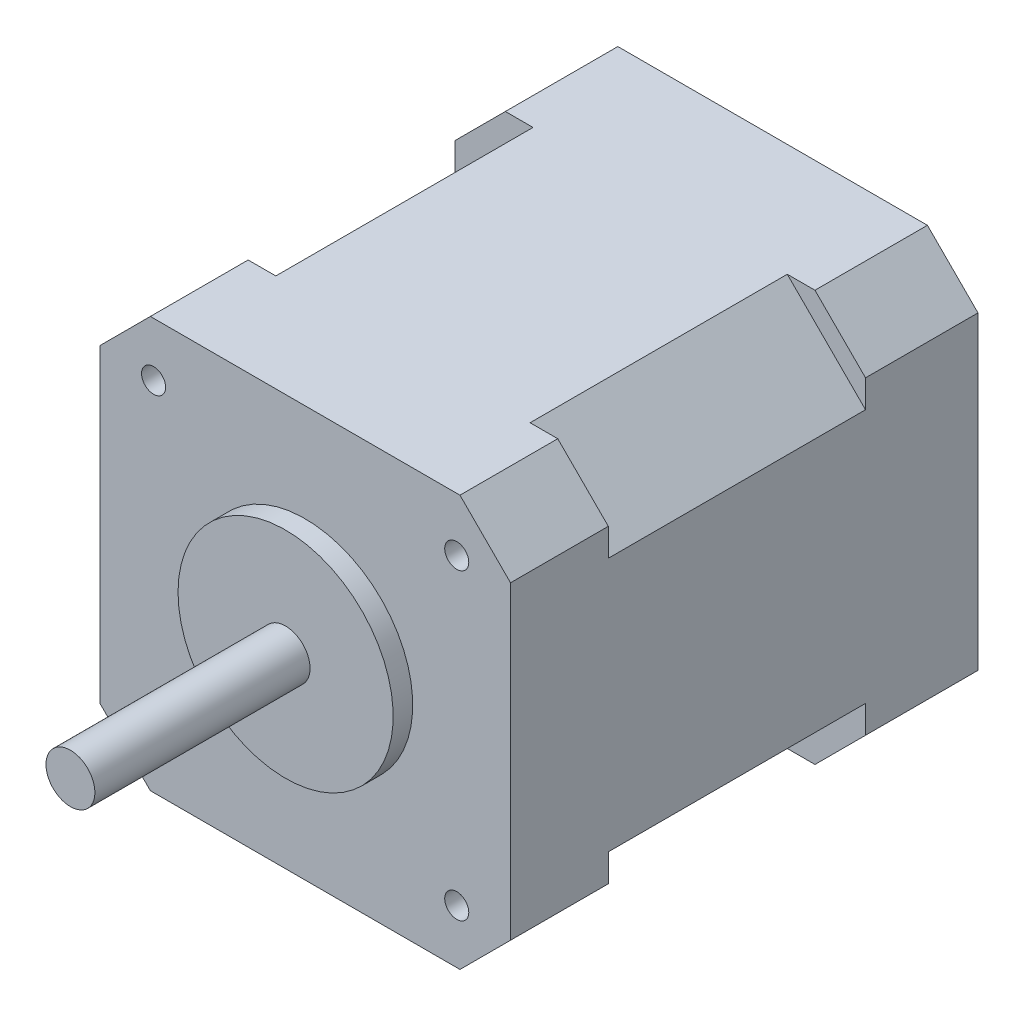
SolidWorks part; units mm, degrees
ref_plane "Front Plane" through (0, 0, 0) normal (0, 0, 1) x (1, 0, 0)
ref_plane "Top Plane" through (0, 0, 0) normal (0, 1, 0) x (1, 0, 0)
ref_plane "Right Plane" through (0, 0, 0) normal (1, 0, 0) x (0, 0, -1)
ref_plane "Plane1" through (0, 0, 0) normal (0, 0, -1) x (-1, 0, 0)
sketch "Sketch1" plane through (0, 0, 0) normal (0, 0, -1) x (-1, 0, 0)
  line L0 (-15.8284, 21) -> (-21, 15.8284)
  line L1 (-21, 15.8284) -> (-21, -15.8284)
  line L2 (-21, -15.8284) -> (-15.8284, -21)
  line L3 (-15.8284, -21) -> (15.8284, -21)
  line L4 (15.8284, -21) -> (21, -15.8284)
  line L5 (21, -15.8284) -> (21, 15.8284)
  line L6 (21, 15.8284) -> (15.8284, 21)
  line L7 (15.8284, 21) -> (-15.8284, 21)
extrude "Boss-Extrude1" add sketch "Sketch1" against normal blind 11.5
sketch "Sketch2" plane through (0, 0, 11.5) normal (0, 0, 1) x (1, 0, 0)
  line L0 (13, -21) -> (-13, -21)
  line L1 (-13, -21) -> (-21, -13)
  line L2 (-21, -13) -> (-21, 13)
  line L3 (-21, 13) -> (-13, 21)
  line L4 (-13, 21) -> (13, 21)
  line L5 (13, 21) -> (21, 13)
  line L6 (21, 13) -> (21, -13)
  line L7 (21, -13) -> (13, -21)
extrude "Boss-Extrude2" add sketch "Sketch2" along normal blind 26.3
sketch "Sketch3" plane through (0, 0, 37.8) normal (0, 0, 1) x (1, 0, 0)
  line L0 (15.8284, 21) -> (21, 15.8284)
  line L1 (21, 15.8284) -> (21, -15.8284)
  line L2 (21, -15.8284) -> (15.8284, -21)
  line L3 (15.8284, -21) -> (-15.8284, -21)
  line L4 (-15.8284, -21) -> (-21, -15.8284)
  line L5 (-21, -15.8284) -> (-21, 15.8284)
  line L6 (-21, 15.8284) -> (-15.8284, 21)
  line L7 (-15.8284, 21) -> (15.8284, 21)
extrude "Boss-Extrude3" add sketch "Sketch3" along normal blind 10
ref_plane "Plane2" through (0, 0, 3.65) normal (0, 0, 1) x (1, 0, 0)
sketch "Sketch4" plane through (0, 0, 3.65) normal (0, 0, 1) x (1, 0, 0)
  line L0 (-31, 1.25) -> (-31, 0.65)
  line L1 (-31, 0.65) -> (-21, 0.65)
  line L2 (-21, 0.65) -> (-21, 1.25)
  line L3 (-21, 1.25) -> (-31, 1.25)
  line L4 (-31, 0.65) -> (-21, 0.65) construction
revolve "Revolve1" add sketch "Sketch4" angle 360 about L4
sketch "Sketch5" plane through (0, 0, 3.65) normal (0, 0, 1) x (1, 0, 0)
  line L0 (-31, -0.05) -> (-31, -0.65)
  line L1 (-31, -0.65) -> (-21, -0.65)
  line L2 (-21, -0.65) -> (-21, -0.05)
  line L3 (-21, -0.05) -> (-31, -0.05)
  line L4 (-31, -0.65) -> (-21, -0.65) construction
revolve "Revolve2" add sketch "Sketch5" angle 360 about L4
ref_plane "Plane3" through (0, 0, 4.95) normal (0, 0, 1) x (1, 0, 0)
sketch "Sketch6" plane through (0, 0, 4.95) normal (0, 0, 1) x (1, 0, 0)
  line L0 (-31, -0.05) -> (-31, -0.65)
  line L1 (-31, -0.65) -> (-21, -0.65)
  line L2 (-21, -0.65) -> (-21, -0.05)
  line L3 (-21, -0.05) -> (-31, -0.05)
  line L4 (-31, -0.65) -> (-21, -0.65) construction
revolve "Revolve3" add sketch "Sketch6" angle 360 about L4
sketch "Sketch7" plane through (0, 0, 4.95) normal (0, 0, 1) x (1, 0, 0)
  line L0 (-31, 1.25) -> (-31, 0.65)
  line L1 (-31, 0.65) -> (-21, 0.65)
  line L2 (-21, 0.65) -> (-21, 1.25)
  line L3 (-21, 1.25) -> (-31, 1.25)
  line L4 (-31, 0.65) -> (-21, 0.65) construction
revolve "Revolve4" add sketch "Sketch7" angle 360 about L4
ref_plane "Plane4" through (0, 0, 0) normal (0, -1, 0) x (1, 0, 0)
sketch "Sketch8" plane through (0, 0, 0) normal (0, -1, 0) x (1, 0, 0)
  line L0 (2.5, 71.8) -> (0, 71.8)
  line L1 (0, 71.8) -> (0, 47.8)
  line L2 (0, 47.8) -> (11, 47.8)
  line L3 (11, 47.8) -> (11, 49.8)
  line L4 (11, 49.8) -> (2.5, 49.8)
  line L5 (2.5, 49.8) -> (2.5, 71.8)
  line L6 (0, 71.8) -> (0, 47.8) construction
revolve "Revolve5" add sketch "Sketch8" angle 360 about L6
hole_wizard "Hole1" positions "Sketch10" profile "Sketch9" legacy
sketch "Sketch10" plane through (0, 0, 47.8) normal (0, 0, 1) x (1, 0, 0)
  point P0 (-15.5, 15.5)
sketch "Sketch9" plane through (-15.5, 15.5, 47.8) normal (1, 0, 0) x (0, -1, 0)
  line L0 (0, 0) -> (0, 5)
  line L1 (0, 5) -> (1.2295, 5)
  line L2 (1.2295, 5) -> (1.2295, 0)
  line L3 (1.2295, 0) -> (0, 0)
  line L4 (0, 110) -> (0, -10) construction
  dimension "Diameter" = 2.459
  dimension "Depth" = 5
hole_wizard "Hole2" positions "Sketch12" profile "Sketch11" legacy
sketch "Sketch12" plane through (0, 0, 47.8) normal (0, 0, 1) x (1, 0, 0)
  point P0 (-15.5, -15.5)
sketch "Sketch11" plane through (-15.5, -15.5, 47.8) normal (1, 0, 0) x (0, -1, 0)
  line L0 (0, 0) -> (0, 5)
  line L1 (0, 5) -> (1.2295, 5)
  line L2 (1.2295, 5) -> (1.2295, 0)
  line L3 (1.2295, 0) -> (0, 0)
  line L4 (0, 110) -> (0, -10) construction
  dimension "Diameter" = 2.459
  dimension "Depth" = 5
hole_wizard "Hole3" positions "Sketch14" profile "Sketch13" legacy
sketch "Sketch14" plane through (0, 0, 47.8) normal (0, 0, 1) x (1, 0, 0)
  point P0 (15.5, 15.5)
sketch "Sketch13" plane through (15.5, 15.5, 47.8) normal (1, 0, 0) x (0, -1, 0)
  line L0 (0, 0) -> (0, 5)
  line L1 (0, 5) -> (1.2295, 5)
  line L2 (1.2295, 5) -> (1.2295, 0)
  line L3 (1.2295, 0) -> (0, 0)
  line L4 (0, 110) -> (0, -10) construction
  dimension "Diameter" = 2.459
  dimension "Depth" = 5
hole_wizard "Hole4" positions "Sketch16" profile "Sketch15" legacy
sketch "Sketch16" plane through (0, 0, 47.8) normal (0, 0, 1) x (1, 0, 0)
  point P0 (15.5, -15.5)
sketch "Sketch15" plane through (15.5, -15.5, 47.8) normal (1, 0, 0) x (0, -1, 0)
  line L0 (0, 0) -> (0, 5)
  line L1 (0, 5) -> (1.2295, 5)
  line L2 (1.2295, 5) -> (1.2295, 0)
  line L3 (1.2295, 0) -> (0, 0)
  line L4 (0, 110) -> (0, -10) construction
  dimension "Diameter" = 2.459
  dimension "Depth" = 5
